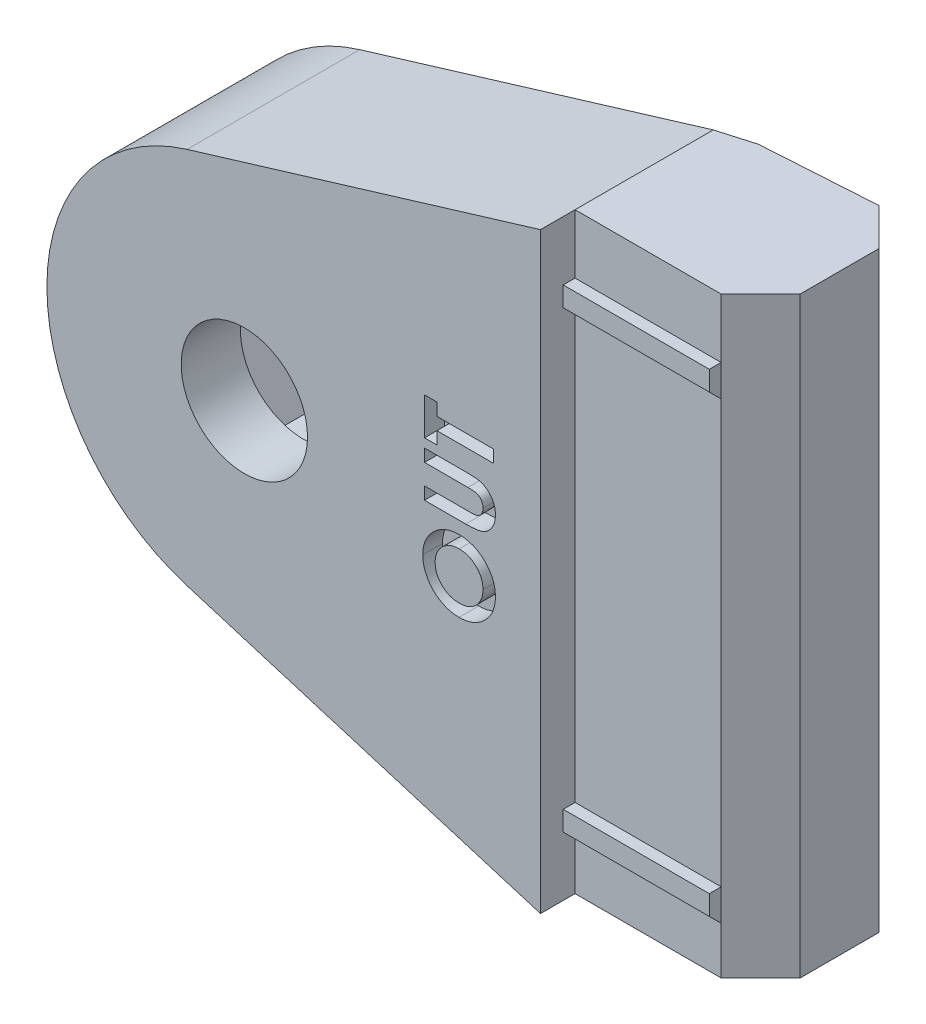
SolidWorks part; units mm, degrees
ref_plane "Alzado" through (0, 0, 0) normal (0, 0, 1) x (1, 0, 0)
ref_plane "Planta" through (0, 0, 0) normal (0, 1, 0) x (1, 0, 0)
ref_plane "Vista lateral" through (0, 0, 0) normal (1, 0, 0) x (0, 0, -1)
sketch "Croquis1" plane through (0, 0, 0) normal (0, 1, 0) x (1, 0, 0)
  line L0 (0, 0) -> (-30, 0)
  line L1 (-30, 0) -> (-30, 8)
  line L2 (-30, 8) -> (-1.75, 8) construction
  line L3 (-1.75, 8) -> (0, 9.75) construction
  line L4 (0, 9.75) -> (9.4, 9.75)
  line L5 (9.4, 9.75) -> (9.4, 1.75)
  line L6 (9.4, 1.75) -> (0, 1.75)
  line L7 (0, 1.75) -> (0, 0)
  line L8 (-15, 18.5318) -> (-15, -3.9407) construction
  line L9 (-30, 8) -> (-30, 9.75)
  line L10 (-30, 9.75) -> (0, 9.75)
  dimension "D1" = 1.75
  dimension "D2" = 30
  dimension "D3" = 8
  dimension "D4" = 9.4
  dimension "D5" = 15
  dimension "D6" = 45
extrude "Saliente-Extruir1" add sketch "Croquis1" along normal mid plane 30
sketch "Croquis2" plane through (0, 0, 0) normal (0, 0, 1) x (1, 0, 0)
  line L0 (0, 0) -> (-50000, 0) construction
  circle A0 centre (-15, 0) radius 3.2
  dimension "D2" = 6.4
  dimension "D1" = 15
extrude "Cortar-Extruir1" cut sketch "Croquis2" against normal through all
sketch "Croquis3" plane through (0, 0, 0) normal (0, 0, 1) x (1, 0, 0)
  line L1 (-9.2265, 0) -> (-12.1132, 5)
  line L2 (-12.1132, 5) -> (-17.8868, 5)
  line L3 (-17.8868, 5) -> (-20.7735, 0)
  line L4 (-20.7735, 0) -> (-17.8868, -5)
  line L5 (-17.8868, -5) -> (-12.1132, -5)
  line L6 (-12.1132, -5) -> (-9.2265, 0)
  circle A0 centre (-15, 0) radius 5 construction
  dimension "D1" = 10
extrude "Cortar-Extruir2" cut sketch "Croquis3" against normal blind 5 from offset 3 offset against normal yes
chamfer "Chaflán1" distance 2 angle 45 4 edges at (9.4, 0, -1.75) (9.4, 0, -9.75) (-30, -15, -4.875) (-30, 15, -4.875)
sketch "Croquis5" plane through (0, 0, 0) normal (1, 0, 0) x (0, 0, -1)
  line L0 (0, 0) -> (50000, 0) construction
  line L1 (1.75, 12) -> (1.15, 12)
  line L3 (1.15, 12) -> (1.15, 11)
  line L4 (1.15, 11) -> (1.75, 10.4)
  line L5 (1.75, 10.4) -> (1.75, 12)
  line L6 (7.75, 15) -> (9.75, 15) construction
  line L7 (1.75, -11) -> (1.15, -11)
  line L8 (1.15, -11) -> (1.15, -12)
  line L9 (1.15, -12) -> (1.75, -12.6)
  line L10 (1.75, -12.6) -> (1.75, -11)
  line L11 (9.75, -15) -> (7.75, -15) construction
  line L13 (1.75, 15) -> (1.75, -15) construction
  line L14 (1.75, -15) -> (1.75, 15) construction
  dimension "D1" = 0.6
  dimension "D2" = 1
  dimension "D3" = 1.6
  dimension "D4" = 3
  dimension "D5" = 0.6
  dimension "D6" = 1
  dimension "D7" = 1.6
  dimension "D8" = 3
extrude "Saliente-Extruir3" add sketch "Croquis5" along normal up to vertex (7.4 mm away)
sketch "Croquis7" plane through (0, 0, 0) normal (0, 0, 1) x (1, 0, 0)
  line L0 (-17.9028, 9.5694) -> (0, 15)
  line L1 (0, 15) -> (9.4, 15)
  line L2 (9.4, 15) -> (9.4, -15)
  line L3 (9.4, -15) -> (0, -15)
  line L4 (0, -15) -> (-17.9028, -9.5694)
  arc A0 (-17.9028, 9.5694) -> (-17.9028, -9.5694) centre (-15, 0) ccw
  dimension "D1" = 10
extrude "Cortar-Extruir3" cut sketch "Croquis7" against normal blind 10 flip side to cut
sketch "Croquis8" plane through (0, 0, 0) normal (0, 0, 1) x (1, 0, 0)
  line L0 (-2.374, -4.2934) -> (-2.374, 10.4961) construction
  text T0 "<b>OUT</b>"
extrude "Cortar-Extruir4" cut sketch "Croquis8" against normal blind 1
chamfer "Chaflán2" distance 1 angle 45 3 edges at (-8.9514, 12.2847, -9.75) (-25, 0, -9.75) (-8.9514, -12.2847, -9.75)
sketch "Croquis9" plane through (0, 15, 0) normal (0, 1, 0) x (1, 0, 0)
  line L0 (0, 9.15) -> (0, 9.75)
  line L1 (-17.6125, 9.75) -> (3.445, 9.75) construction
  line L2 (0, 9.75) -> (9.3824, 9.75)
  line L3 (9.3824, 9.75) -> (0, 9.15)
  dimension "D1" = 0.6
extrude "Cortar-Extruir5" cut sketch "Croquis9" against normal through all
